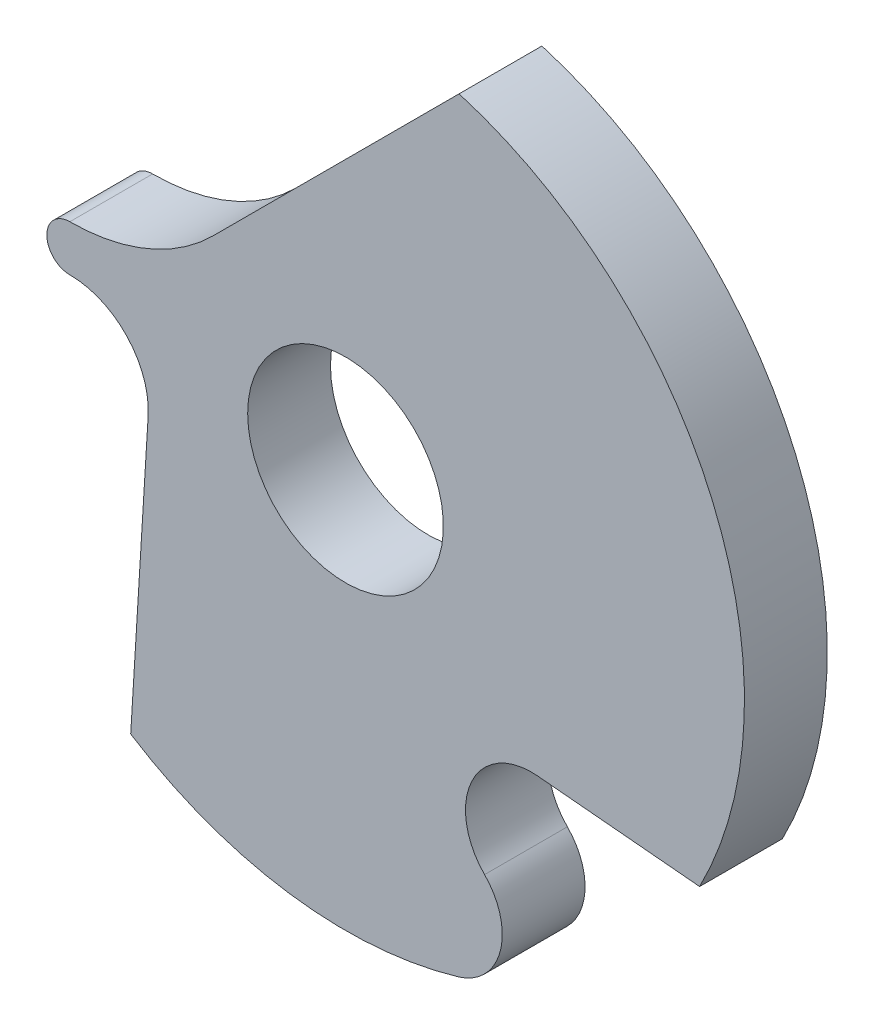
SolidWorks part; units mm, degrees
ref_plane "Alzado" through (0, 0, 0) normal (0, 0, 1) x (1, 0, 0)
ref_plane "Planta" through (0, 0, 0) normal (0, 1, 0) x (1, 0, 0)
ref_plane "Vista lateral" through (0, 0, 0) normal (1, 0, 0) x (0, 0, -1)
ref_plane "Plane1" through (0, 0, 0.55) normal (0, 0, 1) x (1, 0, 0)
sketch "Sketch1" plane through (0, 0, 0.55) normal (0, 0, 1) x (1, 0, 0)
  line L0 (1.2742, -1.1227) -> (2.3519, -1.2211)
  line L1 (0.7544, 2.5404) -> (-0.8807, 0.9053)
  line L2 (-1.3111, -0.347) -> (-1.427, -2.233)
  line L3 (0, -1000.0843) -> (0, 48999.9157) construction
  line L4 (-1000.0538, 0) -> (48999.9462, 0) construction
  line L5 (-1001.8851, 0.3588) -> (48998.1149, 0.3588) construction
  line L6 (-1001.8851, -0.3151) -> (48998.1149, -0.3151) construction
  line L7 (-1001.8851, 1.8559) -> (48998.1149, 1.8559) construction
  line L8 (-998.8194, -1.5585) -> (49001.1806, -1.5585) construction
  line L9 (-999.4188, -2.1522) -> (49000.5812, -2.1522) construction
  line L10 (-1.8313, -999.7254) -> (-1.8313, 49000.2746) construction
  line L11 (0.6351, -1002.2365) -> (0.6351, 48997.7635) construction
  line L12 (1.2345, -1001.6428) -> (1.2345, 48998.3572) construction
  arc A0 (0.75, -2.5417) -> (0.9235, -1.8665) centre (0.6351, -2.1522) ccw
  arc A1 (0.9235, -1.8665) -> (1.2742, -1.1227) centre (1.2345, -1.5585) cw
  arc A2 (2.3519, -1.2211) -> (0.7544, 2.5404) centre (0, 0) ccw
  arc A3 (-0.8807, 0.9053) -> (-1.8313, 0.5115) centre (-1.8313, 1.8559) cw
  arc A4 (-1.8313, 0.5115) -> (-1.8313, 0.2061) centre (-1.8313, 0.3588) ccw
  arc A5 (-1.8313, 0.2061) -> (-1.3111, -0.347) centre (-1.8313, -0.3151) cw
  arc A6 (-1.427, -2.233) -> (0.75, -2.5417) centre (0, 0) ccw
  circle A7 centre (0, 0) radius 0.65
  point P17 (0, 0)
  dimension "D1" = 2
  dimension "D2" = 2
  dimension "D3" = 0.3151
  dimension "D4" = 1.5585
  dimension "D5" = 2.1522
  dimension "D6" = 0.3588
  dimension "D7" = 1.8559
  dimension "D8" = 0.6351
  dimension "D11" = 1.3
  dimension "D12" = 0.1527
  dimension "D9" = 1.2345
  dimension "D10" = 1.8313
  dimension "D13" = 45
  dimension "D14" = 86.484
  dimension "D15" = 5.215
extrude "Boss-Extrude1" add sketch "Sketch1" against normal blind 0.55
